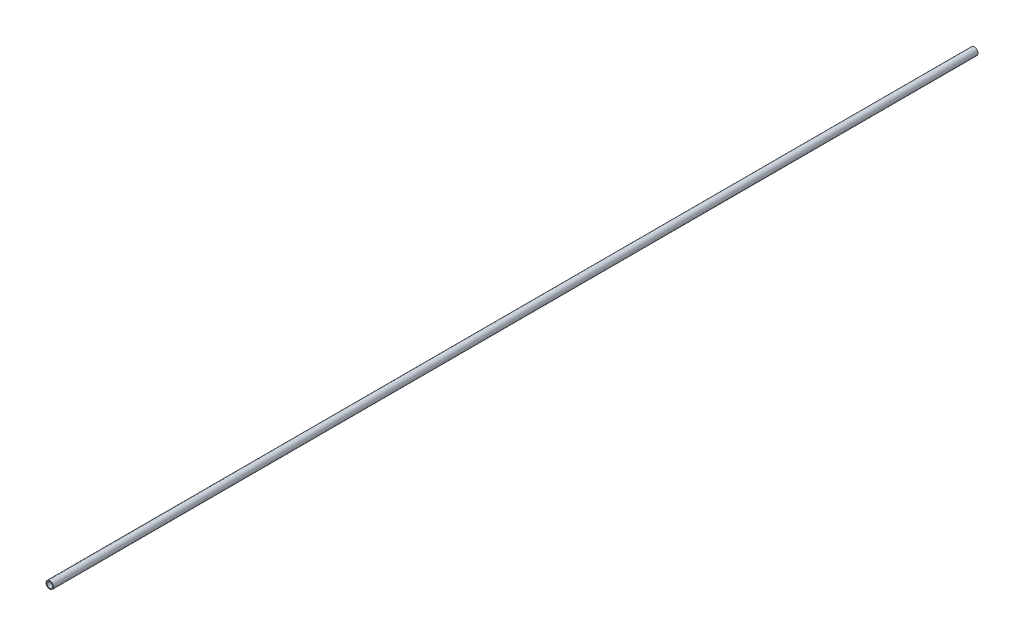
SolidWorks part; units mm, degrees
ref_plane "Plano frontal" through (0, 0, 0) normal (0, 0, 1) x (1, 0, 0)
ref_plane "Plano superior" through (0, 0, 0) normal (0, 1, 0) x (1, 0, 0)
ref_plane "Plano direito" through (0, 0, 0) normal (1, 0, 0) x (0, 0, -1)
sketch "Esboço1" plane through (0, 0, 0) normal (0, 0, 1) x (1, 0, 0)
  circle A0 centre (0, 0) radius 3
  circle A1 centre (0, 0) radius 4
  dimension "D1" = 6
  dimension "D2" = 8
extrude "Ressalto-extrusão1" add sketch "Esboço1" along normal blind 1000
